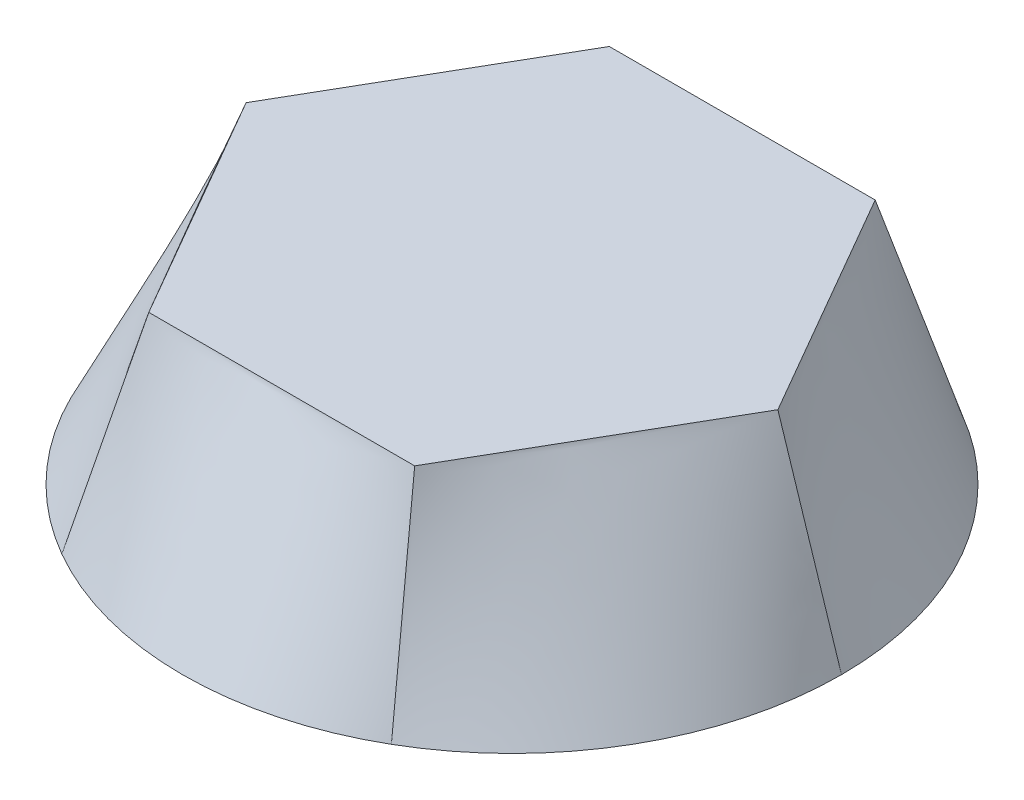
SolidWorks part; units mm, degrees
ref_plane "Front Plane" through (0, 0, 0) normal (0, 0, 1) x (1, 0, 0)
ref_plane "Top Plane" through (0, 0, 0) normal (0, 1, 0) x (1, 0, 0)
ref_plane "Right Plane" through (0, 0, 0) normal (1, 0, 0) x (0, 0, -1)
sketch "Sketch1" plane through (0, 0, 0) normal (0, 1, 0) x (1, 0, 0)
  circle A0 centre (0, 0) radius 25
  dimension "D1" = 50
ref_plane "Plane1" through (0, 15, 0) normal (0, 1, 0) x (1, 0, 0)
sketch "Sketch2" plane through (0, 15, 0) normal (0, 1, 0) x (1, 0, 0)
  line L1 (20.1725, 0) -> (10.0863, 17.4699)
  line L2 (10.0863, 17.4699) -> (-10.0863, 17.4699)
  line L3 (-10.0863, 17.4699) -> (-20.1725, 0)
  line L4 (-20.1725, 0) -> (-10.0863, -17.4699)
  line L5 (-10.0863, -17.4699) -> (10.0863, -17.4699)
  line L6 (10.0863, -17.4699) -> (20.1725, 0)
  circle A0 centre (0, 0) radius 17.4699 construction
  point P1 (28.8701, 0)
  point P10 (0, 0)
  point P11 (-20.1725, 0)
loft "Loft1" add profiles "Sketch1", "Sketch2"
